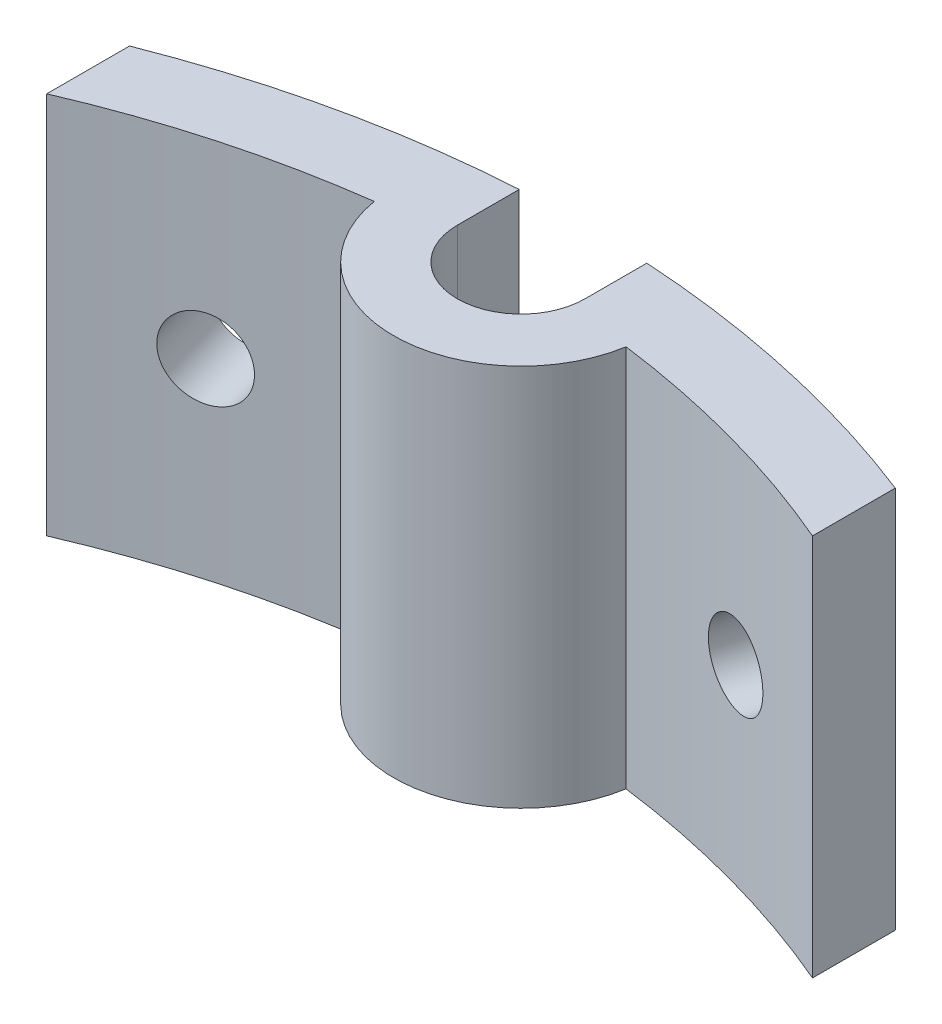
SolidWorks part; units mm, degrees
ref_plane "Plan de face" through (0, 0, 0) normal (0, 0, 1) x (1, 0, 0)
ref_plane "Plan de dessus" through (0, 0, 0) normal (0, 1, 0) x (1, 0, 0)
ref_plane "Plan de droite" through (0, 0, 0) normal (1, 0, 0) x (0, 0, -1)
sketch "Esquisse1" plane through (0, 0, 0) normal (0, 1, 0) x (1, 0, 0)
  line L0 (0, 0) -> (0, 53.3057) construction
  line L1 (0, 0) -> (-55.1604, 0) construction
  line L2 (0, 0) -> (77.1938, 0) construction
  line L3 (15, 0) -> (15, 47.791) construction
  line L4 (-15, 0) -> (-15, 47.791) construction
  line L5 (-2.5, 38.5) -> (-2.5, 40.9237)
  line L6 (2.5, 38.5) -> (2.5, 40.9237)
  line L7 (-15, 38.1576) -> (-15, 34.9142)
  line L8 (15, 38.1576) -> (15, 34.9142)
  circle A0 centre (0, 0) radius 41 construction
  circle A1 centre (0, 38.5) radius 2.5 construction
  arc A2 (-15, 38.1576) -> (-2.5, 40.9237) centre (0, 0) cw
  arc A3 (-15, 34.9142) -> (-4.9321, 37.6786) centre (0, 0) cw
  arc A4 (2.5, 40.9237) -> (15, 38.1576) centre (0, 0) cw
  arc A5 (15, 34.9142) -> (4.9321, 37.6786) centre (0, 0) ccw
  arc A6 (-2.5, 38.5) -> (2.5, 38.5) centre (0, 38.5) ccw
  arc A7 (0, 33.5) -> (-4.9321, 37.6786) centre (0, 38.5) cw
  arc A8 (0, 33.5) -> (4.9321, 37.6786) centre (0, 38.5) ccw
  dimension "D1" = 82
  dimension "D2" = 5
  dimension "D3" = 38.5
  dimension "D4" = 38
  dimension "D5" = 38
  dimension "D6" = 5
  dimension "D7" = 15
  dimension "D8" = 15
  dimension "D9" = 0
extrude "Boss.-Extru.1" add sketch "Esquisse1" along normal blind 15
hole_wizard "Dégagement M41" positions "Esquisse3D1" profile "Esquisse2" hole size "M4" standard "ISO"
sketch3d "Esquisse3D1"
  line L0 (-15, 15, -38.1576) -> (-15, 0, -38.1576) construction
  line L1 (15, 15, -38.1576) -> (15, 0, -38.1576) construction
  point P0 (-11.2104, 7.5, -39.4376)
  point P2 (11.2104, 7.5, -39.4376)
  dimension "D1" = 4
  dimension "D2" = 4
  dimension "D3" = 7.5
  dimension "D4" = 7.5
sketch "Esquisse2" plane through (-11.2104, 7.5, -39.4376) normal (0, 1, 0) x (-0.9619, 0, 0.2734)
  line L0 (0, 0) -> (0, 30.9313)
  line L1 (0, 30.9313) -> (1.55, 30)
  line L2 (1.55, 30) -> (1.55, 0)
  line L5 (1.55, 0) -> (0, 0)
  line L10 (0, 30.9313) -> (-1.55, 30) construction
  line L11 (0, -6.35) -> (0, 107.95) construction
  dimension "Diamètre du perçage" = 3.1
  dimension "Profondeur du perçage" = 30
  dimension "Angle de pointe" = 118
